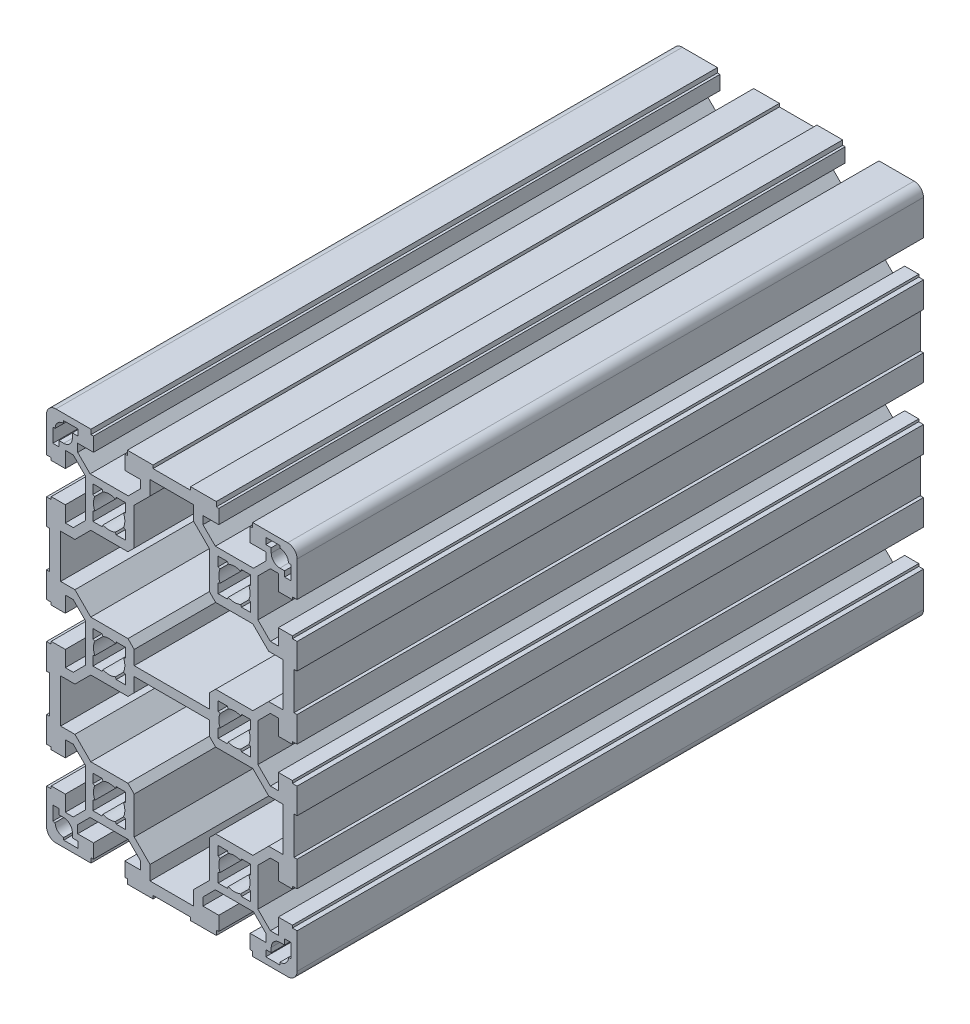
SolidWorks part; units mm, degrees
ref_plane "Front Plane" through (0, 0, 0) normal (0, 0, 1) x (1, 0, 0)
ref_plane "Top Plane" through (0, 0, 0) normal (0, 1, 0) x (1, 0, 0)
ref_plane "Right Plane" through (0, 0, 0) normal (1, 0, 0) x (0, 0, -1)
sketch "Sketch1" plane through (0, 0, 0) normal (0, 0, 1) x (1, 0, 0)
  line L0 (27.5, 46.0858) -> (31.4642, 50.05)
  line L1 (31.4642, 50.05) -> (34, 50.05)
  line L2 (34, 50.05) -> (34, 45)
  line L3 (34, 45) -> (38.5, 45)
  line L4 (38.5, 45) -> (38.5, 45.8)
  line L5 (38.5, 45.8) -> (40, 45.8)
  line L6 (40, 45.8) -> (40, 57)
  line L7 (37, 60) -> (25.8, 60)
  line L8 (25.8, 60) -> (25.8, 58.5)
  line L9 (25.8, 58.5) -> (25, 58.5)
  line L10 (25, 58.5) -> (25, 54)
  line L11 (25, 54) -> (30.05, 54)
  line L12 (30.05, 54) -> (30.05, 51.4642)
  line L13 (30.05, 51.4642) -> (26.0858, 47.5)
  line L14 (26.0858, 47.5) -> (13.9142, 47.5)
  line L15 (13.9142, 47.5) -> (9.95, 51.4642)
  line L16 (9.95, 51.4642) -> (9.95, 54)
  line L17 (9.95, 54) -> (15, 54)
  line L18 (15, 54) -> (15, 58.5)
  line L19 (15, 58.5) -> (14.2, 58.5)
  line L20 (14.2, 58.5) -> (14.2, 60)
  line L21 (14.2, 60) -> (6, 60)
  line L22 (6, 60) -> (6, 59)
  line L23 (27.5, -6.0858) -> (27.5, 6.0858)
  line L24 (27.5, 6.0858) -> (31.4642, 10.05)
  line L25 (31.4642, 10.05) -> (34, 10.05)
  line L26 (34, 10.05) -> (34, 5)
  line L27 (34, 5) -> (38.5, 5)
  line L28 (38.5, 5) -> (38.5, 5.8)
  line L29 (38.5, 5.8) -> (40, 5.8)
  line L30 (40, 5.8) -> (40, 14)
  line L31 (40, 14) -> (39, 14)
  line L32 (39, 14) -> (39, 26)
  line L33 (39, 26) -> (40, 26)
  line L34 (40, 26) -> (40, 34.2)
  line L35 (40, 34.2) -> (38.5, 34.2)
  line L36 (38.5, 34.2) -> (38.5, 35)
  line L37 (38.5, 35) -> (34, 35)
  line L38 (34, 35) -> (34, 29.95)
  line L39 (34, 29.95) -> (31.4642, 29.95)
  line L40 (31.4642, 29.95) -> (27.5, 33.9142)
  line L41 (27.5, 33.9142) -> (27.5, 46.0858)
  line L42 (12, 45.8787) -> (6.95, 50.9287)
  line L43 (6.95, 50.9287) -> (6.95, 55.5)
  line L44 (12, 1.5) -> (12, 6)
  line L45 (12, 6) -> (14, 8)
  line L46 (14, 8) -> (25.8787, 8)
  line L47 (25.8787, 8) -> (30.9287, 13.05)
  line L48 (30.9287, 13.05) -> (35.5, 13.05)
  line L49 (35.5, 13.05) -> (35.5, 26.95)
  line L50 (35.5, 26.95) -> (30.9287, 26.95)
  line L51 (-14.8, 2.2603) -> (-15.4145, 1.9932)
  line L52 (-14.8, 5.2) -> (-14.8, 2.2603)
  line L53 (-17.7397, 5.2) -> (-14.8, 5.2)
  line L54 (-18.0068, 4.5855) -> (-17.7397, 5.2)
  line L55 (-22.2603, 5.2) -> (-21.9932, 4.5855)
  line L56 (-25.2, 5.2) -> (-22.2603, 5.2)
  line L57 (-25.2, 2.2603) -> (-25.2, 5.2)
  line L58 (-24.5855, 1.9932) -> (-25.2, 2.2603)
  line L59 (30.9287, 26.95) -> (25.8787, 32)
  line L60 (25.8787, 32) -> (14, 32)
  line L61 (14, 32) -> (12, 34)
  line L62 (12, 34) -> (12, 45.8787)
  line L63 (34.5, 51.75) -> (36, 51.75)
  line L64 (36, 51.75) -> (36, 50)
  line L65 (36, 50) -> (38, 50)
  line L66 (38, 50) -> (38, 54.5)
  line L67 (38, 54.5) -> (37.25, 54.5)
  line L68 (34.5, 57.25) -> (34.5, 58)
  line L69 (34.5, 58) -> (30, 58)
  line L70 (30, 58) -> (30, 56)
  line L71 (30, 56) -> (31.75, 56)
  line L72 (31.75, 56) -> (31.75, 54.5)
  line L73 (17.7397, 34.8) -> (18.0068, 35.4145)
  line L74 (21.9932, 35.4145) -> (22.2603, 34.8)
  line L75 (22.2603, 34.8) -> (25.2, 34.8)
  line L76 (25.2, 34.8) -> (25.2, 37.7397)
  line L77 (25.2, 37.7397) -> (24.5855, 38.0068)
  line L78 (24.5855, 41.9932) -> (25.2, 42.2603)
  line L79 (25.2, 42.2603) -> (25.2, 45.2)
  line L80 (-14.8, 34.8) -> (-17.7397, 34.8)
  line L81 (-14.8, 37.7397) -> (-14.8, 34.8)
  line L82 (-15.4145, 38.0068) -> (-14.8, 37.7397)
  line L83 (-14.8, 42.2603) -> (-15.4145, 41.9932)
  line L84 (-14.8, 45.2) -> (-14.8, 42.2603)
  line L85 (-17.7397, 45.2) -> (-14.8, 45.2)
  line L86 (-18.0068, 44.5855) -> (-17.7397, 45.2)
  line L87 (-22.2603, 45.2) -> (-21.9932, 44.5855)
  line L88 (-25.2, 45.2) -> (-22.2603, 45.2)
  line L89 (-25.2, 42.2603) -> (-25.2, 45.2)
  line L90 (-24.5855, 41.9932) -> (-25.2, 42.2603)
  line L91 (-25.2, 37.7397) -> (-24.5855, 38.0068)
  line L92 (-25.2, 34.8) -> (-25.2, 37.7397)
  line L93 (-22.2603, 34.8) -> (-25.2, 34.8)
  line L94 (-21.9932, 35.4145) -> (-22.2603, 34.8)
  line L95 (-17.7397, 34.8) -> (-18.0068, 35.4145)
  line L96 (25.2, 45.2) -> (22.2603, 45.2)
  line L97 (22.2603, 45.2) -> (21.9932, 44.5855)
  line L98 (18.0068, 44.5855) -> (17.7397, 45.2)
  line L99 (17.7397, 45.2) -> (14.8, 45.2)
  line L100 (14.8, 45.2) -> (14.8, 42.2603)
  line L101 (14.8, 42.2603) -> (15.4145, 41.9932)
  line L102 (15.4145, 38.0068) -> (14.8, 37.7397)
  line L103 (14.8, 37.7397) -> (14.8, 34.8)
  line L104 (14.8, 34.8) -> (17.7397, 34.8)
  line L105 (24.5855, 1.9932) -> (25.2, 2.2603)
  line L106 (25.2, 2.2603) -> (25.2, 5.2)
  line L107 (25.2, 5.2) -> (22.2603, 5.2)
  line L108 (22.2603, 5.2) -> (21.9932, 4.5855)
  line L109 (18.0068, 4.5855) -> (17.7397, 5.2)
  line L110 (17.7397, 5.2) -> (14.8, 5.2)
  line L111 (14.8, 5.2) -> (14.8, 2.2603)
  line L112 (14.8, 2.2603) -> (15.4145, 1.9932)
  line L113 (-27.5, -46.0858) -> (-31.4642, -50.05)
  line L114 (-31.4642, -50.05) -> (-34, -50.05)
  line L115 (-34, -50.05) -> (-34, -45)
  line L116 (-34, -45) -> (-38.5, -45)
  line L117 (-38.5, -45) -> (-38.5, -45.8)
  line L118 (-38.5, -45.8) -> (-40, -45.8)
  line L119 (-40, -45.8) -> (-40, -57)
  line L120 (-37, -60) -> (-25.8, -60)
  line L121 (-25.8, -60) -> (-25.8, -58.5)
  line L122 (-25.8, -58.5) -> (-25, -58.5)
  line L123 (-25, -58.5) -> (-25, -54)
  line L124 (-25, -54) -> (-30.05, -54)
  line L125 (-30.05, -54) -> (-30.05, -51.4642)
  line L126 (-31.75, 56) -> (-31.75, 54.5)
  line L127 (-30, 56) -> (-31.75, 56)
  line L128 (-30, 58) -> (-30, 56)
  line L129 (-34.5, 58) -> (-30, 58)
  line L130 (-34.5, 57.25) -> (-34.5, 58)
  line L131 (-38, 54.5) -> (-37.25, 54.5)
  line L132 (-38, 50) -> (-38, 54.5)
  line L133 (-36, 50) -> (-38, 50)
  line L134 (-36, 51.75) -> (-36, 50)
  line L135 (-34.5, 51.75) -> (-36, 51.75)
  line L136 (-30.05, -51.4642) -> (-26.0858, -47.5)
  line L137 (-26.0858, -47.5) -> (-13.9142, -47.5)
  line L138 (-13.9142, -47.5) -> (-9.95, -51.4642)
  line L139 (-9.95, -51.4642) -> (-9.95, -54)
  line L140 (-9.95, -54) -> (-15, -54)
  line L141 (-15, -54) -> (-15, -58.5)
  line L142 (-15, -58.5) -> (-14.2, -58.5)
  line L143 (-14.2, -58.5) -> (-14.2, -60)
  line L144 (-14.2, -60) -> (-6, -60)
  line L145 (-6, -60) -> (-6, -59)
  line L146 (-6, -59) -> (6, -59)
  line L147 (-27.5, -6.0858) -> (-31.4642, -10.05)
  line L148 (-31.4642, -10.05) -> (-34, -10.05)
  line L149 (-34, -10.05) -> (-34, -5)
  line L150 (-34, -5) -> (-38.5, -5)
  line L151 (-38.5, -5) -> (-38.5, -5.8)
  line L152 (-38.5, -5.8) -> (-40, -5.8)
  line L153 (-40, -5.8) -> (-40, -14)
  line L154 (-40, -14) -> (-39, -14)
  line L155 (-39, -14) -> (-39, -26)
  line L156 (-39, -26) -> (-40, -26)
  line L157 (-40, -26) -> (-40, -34.2)
  line L158 (-40, -34.2) -> (-38.5, -34.2)
  line L159 (-38.5, -34.2) -> (-38.5, -35)
  line L160 (-38.5, -35) -> (-34, -35)
  line L161 (-34, -35) -> (-34, -29.95)
  line L162 (-34, -29.95) -> (-31.4642, -29.95)
  line L163 (-31.4642, -29.95) -> (-27.5, -33.9142)
  line L164 (-12, 34) -> (-12, 45.8787)
  line L165 (-14, 32) -> (-12, 34)
  line L166 (-25.8787, 32) -> (-14, 32)
  line L167 (-30.9287, 26.95) -> (-25.8787, 32)
  line L168 (-35.5, 26.95) -> (-30.9287, 26.95)
  line L169 (-35.5, 13.05) -> (-35.5, 26.95)
  line L170 (-30.9287, 13.05) -> (-35.5, 13.05)
  line L171 (-25.8787, 8) -> (-30.9287, 13.05)
  line L172 (-14, 8) -> (-25.8787, 8)
  line L173 (-12, 6) -> (-14, 8)
  line L174 (-12, 1.5) -> (-12, 6)
  line L175 (12, 1.5) -> (-12, 1.5)
  line L176 (-27.5, -33.9142) -> (-27.5, -46.0858)
  line L177 (-12, -45.8787) -> (-6.95, -50.9287)
  line L178 (-6.95, -50.9287) -> (-6.95, -55.5)
  line L179 (-6.95, -55.5) -> (6.95, -55.5)
  line L180 (12, -1.5) -> (-12, -1.5)
  line L181 (-12, -1.5) -> (-12, -6)
  line L182 (-12, -6) -> (-14, -8)
  line L183 (-14, -8) -> (-25.8787, -8)
  line L184 (-25.8787, -8) -> (-30.9287, -13.05)
  line L185 (-30.9287, -13.05) -> (-35.5, -13.05)
  line L186 (-35.5, -13.05) -> (-35.5, -26.95)
  line L187 (-35.5, -26.95) -> (-30.9287, -26.95)
  line L188 (-30.9287, -26.95) -> (-25.8787, -32)
  line L189 (-6.95, 55.5) -> (6.95, 55.5)
  line L190 (-6.95, 50.9287) -> (-6.95, 55.5)
  line L191 (-12, 45.8787) -> (-6.95, 50.9287)
  line L192 (-27.5, 33.9142) -> (-27.5, 46.0858)
  line L193 (-31.4642, 29.95) -> (-27.5, 33.9142)
  line L194 (-34, 29.95) -> (-31.4642, 29.95)
  line L195 (-34, 35) -> (-34, 29.95)
  line L196 (-38.5, 35) -> (-34, 35)
  line L197 (-38.5, 34.2) -> (-38.5, 35)
  line L198 (-40, 34.2) -> (-38.5, 34.2)
  line L199 (-40, 26) -> (-40, 34.2)
  line L200 (-39, 26) -> (-40, 26)
  line L201 (-39, 14) -> (-39, 26)
  line L202 (-40, 14) -> (-39, 14)
  line L203 (-40, 5.8) -> (-40, 14)
  line L204 (-38.5, 5.8) -> (-40, 5.8)
  line L205 (-38.5, 5) -> (-38.5, 5.8)
  line L206 (-34, 5) -> (-38.5, 5)
  line L207 (-34, 10.05) -> (-34, 5)
  line L208 (-31.4642, 10.05) -> (-34, 10.05)
  line L209 (-27.5, 6.0858) -> (-31.4642, 10.05)
  line L210 (-27.5, -6.0858) -> (-27.5, 6.0858)
  line L211 (-25.8787, -32) -> (-14, -32)
  line L212 (-14, -32) -> (-12, -34)
  line L213 (-12, -34) -> (-12, -45.8787)
  line L214 (-34.5, -51.75) -> (-36, -51.75)
  line L215 (-36, -51.75) -> (-36, -50)
  line L216 (-36, -50) -> (-38, -50)
  line L217 (-38, -50) -> (-38, -54.5)
  line L218 (-38, -54.5) -> (-37.25, -54.5)
  line L219 (-34.5, -57.25) -> (-34.5, -58)
  line L220 (-34.5, -58) -> (-30, -58)
  line L221 (-30, -58) -> (-30, -56)
  line L222 (-30, -56) -> (-31.75, -56)
  line L223 (-31.75, -56) -> (-31.75, -54.5)
  line L224 (14.8, -2.2603) -> (15.4145, -1.9932)
  line L225 (14.8, -5.2) -> (14.8, -2.2603)
  line L226 (17.7397, -5.2) -> (14.8, -5.2)
  line L227 (18.0068, -4.5855) -> (17.7397, -5.2)
  line L228 (22.2603, -5.2) -> (21.9932, -4.5855)
  line L229 (25.2, -5.2) -> (22.2603, -5.2)
  line L230 (25.2, -2.2603) -> (25.2, -5.2)
  line L231 (24.5855, -1.9932) -> (25.2, -2.2603)
  line L232 (14.8, -34.8) -> (17.7397, -34.8)
  line L233 (14.8, -37.7397) -> (14.8, -34.8)
  line L234 (15.4145, -38.0068) -> (14.8, -37.7397)
  line L235 (14.8, -42.2603) -> (15.4145, -41.9932)
  line L236 (14.8, -45.2) -> (14.8, -42.2603)
  line L237 (17.7397, -45.2) -> (14.8, -45.2)
  line L238 (18.0068, -44.5855) -> (17.7397, -45.2)
  line L239 (22.2603, -45.2) -> (21.9932, -44.5855)
  line L240 (25.2, -45.2) -> (22.2603, -45.2)
  line L241 (-17.7397, -34.8) -> (-18.0068, -35.4145)
  line L242 (-21.9932, -35.4145) -> (-22.2603, -34.8)
  line L243 (-22.2603, -34.8) -> (-25.2, -34.8)
  line L244 (-25.2, -34.8) -> (-25.2, -37.7397)
  line L245 (-25.2, -37.7397) -> (-24.5855, -38.0068)
  line L246 (-24.5855, -41.9932) -> (-25.2, -42.2603)
  line L247 (-25.2, -42.2603) -> (-25.2, -45.2)
  line L248 (-25.2, -45.2) -> (-22.2603, -45.2)
  line L249 (-22.2603, -45.2) -> (-21.9932, -44.5855)
  line L250 (-18.0068, -44.5855) -> (-17.7397, -45.2)
  line L251 (-17.7397, -45.2) -> (-14.8, -45.2)
  line L252 (-14.8, -45.2) -> (-14.8, -42.2603)
  line L253 (-14.8, -42.2603) -> (-15.4145, -41.9932)
  line L254 (-15.4145, -38.0068) -> (-14.8, -37.7397)
  line L255 (-14.8, -37.7397) -> (-14.8, -34.8)
  line L256 (-14.8, -34.8) -> (-17.7397, -34.8)
  line L257 (25.2, -42.2603) -> (25.2, -45.2)
  line L258 (24.5855, -41.9932) -> (25.2, -42.2603)
  line L259 (25.2, -37.7397) -> (24.5855, -38.0068)
  line L260 (25.2, -34.8) -> (25.2, -37.7397)
  line L261 (22.2603, -34.8) -> (25.2, -34.8)
  line L262 (21.9932, -35.4145) -> (22.2603, -34.8)
  line L263 (17.7397, -34.8) -> (18.0068, -35.4145)
  line L264 (31.75, -56) -> (31.75, -54.5)
  line L265 (30, -56) -> (31.75, -56)
  line L266 (30, -58) -> (30, -56)
  line L267 (34.5, -58) -> (30, -58)
  line L268 (34.5, -57.25) -> (34.5, -58)
  line L269 (38, -54.5) -> (37.25, -54.5)
  line L270 (38, -50) -> (38, -54.5)
  line L271 (36, -50) -> (38, -50)
  line L272 (36, -51.75) -> (36, -50)
  line L273 (34.5, -51.75) -> (36, -51.75)
  line L274 (12, -34) -> (12, -45.8787)
  line L275 (14, -32) -> (12, -34)
  line L276 (25.8787, -32) -> (14, -32)
  line L277 (30.9287, -26.95) -> (25.8787, -32)
  line L278 (-24.5855, -1.9932) -> (-25.2, -2.2603)
  line L279 (-25.2, -2.2603) -> (-25.2, -5.2)
  line L280 (-25.2, -5.2) -> (-22.2603, -5.2)
  line L281 (-22.2603, -5.2) -> (-21.9932, -4.5855)
  line L282 (-18.0068, -4.5855) -> (-17.7397, -5.2)
  line L283 (-17.7397, -5.2) -> (-14.8, -5.2)
  line L284 (-14.8, -5.2) -> (-14.8, -2.2603)
  line L285 (-14.8, -2.2603) -> (-15.4145, -1.9932)
  line L286 (35.5, -26.95) -> (30.9287, -26.95)
  line L287 (35.5, -13.05) -> (35.5, -26.95)
  line L288 (30.9287, -13.05) -> (35.5, -13.05)
  line L289 (25.8787, -8) -> (30.9287, -13.05)
  line L290 (14, -8) -> (25.8787, -8)
  line L291 (12, -6) -> (14, -8)
  line L292 (12, -1.5) -> (12, -6)
  line L293 (6.95, -50.9287) -> (6.95, -55.5)
  line L294 (12, -45.8787) -> (6.95, -50.9287)
  line L295 (27.5, -33.9142) -> (27.5, -46.0858)
  line L296 (31.4642, -29.95) -> (27.5, -33.9142)
  line L297 (34, -29.95) -> (31.4642, -29.95)
  line L298 (34, -35) -> (34, -29.95)
  line L299 (38.5, -35) -> (34, -35)
  line L300 (38.5, -34.2) -> (38.5, -35)
  line L301 (40, -34.2) -> (38.5, -34.2)
  line L302 (40, -26) -> (40, -34.2)
  line L303 (39, -26) -> (40, -26)
  line L304 (39, -14) -> (39, -26)
  line L305 (40, -14) -> (39, -14)
  line L306 (40, -5.8) -> (40, -14)
  line L307 (38.5, -5.8) -> (40, -5.8)
  line L308 (38.5, -5) -> (38.5, -5.8)
  line L309 (34, -5) -> (38.5, -5)
  line L310 (34, -10.05) -> (34, -5)
  line L311 (31.4642, -10.05) -> (34, -10.05)
  line L312 (27.5, -6.0858) -> (31.4642, -10.05)
  line L313 (6, -60) -> (6, -59)
  line L314 (14.2, -60) -> (6, -60)
  line L315 (14.2, -58.5) -> (14.2, -60)
  line L316 (15, -58.5) -> (14.2, -58.5)
  line L317 (15, -54) -> (15, -58.5)
  line L318 (9.95, -54) -> (15, -54)
  line L319 (9.95, -51.4642) -> (9.95, -54)
  line L320 (13.9142, -47.5) -> (9.95, -51.4642)
  line L321 (26.0858, -47.5) -> (13.9142, -47.5)
  line L322 (30.05, -51.4642) -> (26.0858, -47.5)
  line L323 (30.05, -54) -> (30.05, -51.4642)
  line L324 (25, -54) -> (30.05, -54)
  line L325 (25, -58.5) -> (25, -54)
  line L326 (25.8, -58.5) -> (25, -58.5)
  line L327 (25.8, -60) -> (25.8, -58.5)
  line L328 (37, -60) -> (25.8, -60)
  line L329 (40, -45.8) -> (40, -57)
  line L330 (38.5, -45.8) -> (40, -45.8)
  line L331 (38.5, -45) -> (38.5, -45.8)
  line L332 (34, -45) -> (38.5, -45)
  line L333 (34, -50.05) -> (34, -45)
  line L334 (31.4642, -50.05) -> (34, -50.05)
  line L335 (27.5, -46.0858) -> (31.4642, -50.05)
  line L336 (-6, 59) -> (6, 59)
  line L337 (-6, 60) -> (-6, 59)
  line L338 (-14.2, 60) -> (-6, 60)
  line L339 (-14.2, 58.5) -> (-14.2, 60)
  line L340 (-15, 58.5) -> (-14.2, 58.5)
  line L341 (-15, 54) -> (-15, 58.5)
  line L342 (-9.95, 54) -> (-15, 54)
  line L343 (-9.95, 51.4642) -> (-9.95, 54)
  line L344 (-13.9142, 47.5) -> (-9.95, 51.4642)
  line L345 (-26.0858, 47.5) -> (-13.9142, 47.5)
  line L346 (-30.05, 51.4642) -> (-26.0858, 47.5)
  line L347 (-30.05, 54) -> (-30.05, 51.4642)
  line L348 (-25, 54) -> (-30.05, 54)
  line L349 (-25, 58.5) -> (-25, 54)
  line L350 (-25.8, 58.5) -> (-25, 58.5)
  line L351 (-25.8, 60) -> (-25.8, 58.5)
  line L352 (-37, 60) -> (-25.8, 60)
  line L353 (-40, 45.8) -> (-40, 57)
  line L354 (-38.5, 45.8) -> (-40, 45.8)
  line L355 (-38.5, 45) -> (-38.5, 45.8)
  line L356 (-34, 45) -> (-38.5, 45)
  line L357 (-34, 50.05) -> (-34, 45)
  line L358 (-31.4642, 50.05) -> (-34, 50.05)
  line L359 (-27.5, 46.0858) -> (-31.4642, 50.05)
  line L361 (0, -1.5) -> (0, 87.2985) construction
  line L362 (0, -1.5) -> (0, -80.6537) construction
  arc A0 (37, 60) -> (40, 57) centre (37, 57) cw
  arc A1 (34.5, 57.25) -> (37.25, 54.5) centre (34.5, 54.5) cw
  arc A2 (34.5, 51.75) -> (31.75, 54.5) centre (34.5, 54.5) cw
  arc A3 (21.9932, 35.4145) -> (18.0068, 35.4145) centre (20, 40) cw
  arc A4 (24.5855, 41.9932) -> (24.5855, 38.0068) centre (20, 40) cw
  arc A5 (18.0068, 44.5855) -> (21.9932, 44.5855) centre (20, 40) cw
  arc A6 (15.4145, 38.0068) -> (15.4145, 41.9932) centre (20, 40) cw
  arc A7 (24.5855, 1.9932) -> (24.5855, -1.9932) centre (20, 0) cw
  arc A8 (18.0068, 4.5855) -> (21.9932, 4.5855) centre (20, 0) cw
  arc A9 (15.4145, -1.9932) -> (15.4145, 1.9932) centre (20, 0) cw
  arc A10 (-37, -60) -> (-40, -57) centre (-37, -57) cw
  arc A11 (-34.5, -57.25) -> (-37.25, -54.5) centre (-34.5, -54.5) cw
  arc A12 (-15.4145, -1.9932) -> (-15.4145, 1.9932) centre (-20, 0) ccw
  arc A13 (-18.0068, 4.5855) -> (-21.9932, 4.5855) centre (-20, 0) ccw
  arc A14 (-24.5855, 1.9932) -> (-24.5855, -1.9932) centre (-20, 0) ccw
  arc A15 (-34.5, -51.75) -> (-31.75, -54.5) centre (-34.5, -54.5) cw
  arc A16 (-21.9932, -35.4145) -> (-18.0068, -35.4145) centre (-20, -40) cw
  arc A17 (-24.5855, -41.9932) -> (-24.5855, -38.0068) centre (-20, -40) cw
  arc A18 (-18.0068, -44.5855) -> (-21.9932, -44.5855) centre (-20, -40) cw
  arc A19 (-15.4145, -38.0068) -> (-15.4145, -41.9932) centre (-20, -40) cw
  arc A20 (-15.4145, 38.0068) -> (-15.4145, 41.9932) centre (-20, 40) ccw
  arc A21 (-18.0068, 44.5855) -> (-21.9932, 44.5855) centre (-20, 40) ccw
  arc A22 (-24.5855, 41.9932) -> (-24.5855, 38.0068) centre (-20, 40) ccw
  arc A23 (-21.9932, 35.4145) -> (-18.0068, 35.4145) centre (-20, 40) ccw
  arc A24 (-18.0068, -4.5855) -> (-21.9932, -4.5855) centre (-20, 0) cw
  arc A25 (18.0068, -4.5855) -> (21.9932, -4.5855) centre (20, 0) ccw
  arc A26 (15.4145, -38.0068) -> (15.4145, -41.9932) centre (20, -40) ccw
  arc A27 (18.0068, -44.5855) -> (21.9932, -44.5855) centre (20, -40) ccw
  arc A28 (24.5855, -41.9932) -> (24.5855, -38.0068) centre (20, -40) ccw
  arc A29 (21.9932, -35.4145) -> (18.0068, -35.4145) centre (20, -40) ccw
  arc A30 (-34.5, 51.75) -> (-31.75, 54.5) centre (-34.5, 54.5) ccw
  arc A31 (-34.5, 57.25) -> (-37.25, 54.5) centre (-34.5, 54.5) ccw
  arc A32 (34.5, -51.75) -> (31.75, -54.5) centre (34.5, -54.5) ccw
  arc A33 (34.5, -57.25) -> (37.25, -54.5) centre (34.5, -54.5) ccw
  arc A34 (37, -60) -> (40, -57) centre (37, -57) ccw
  arc A35 (-37, 60) -> (-40, 57) centre (-37, 57) ccw
  point P79 (0, 59)
  point P102 (0, 55.5)
  point P104 (0, 1.5)
  point P227 (0, -55.5)
  point P228 (0, -59)
  point P254 (-27.5, 0)
  point P396 (27.5, 0)
  dimension "D3" = 10
  dimension "D1" = 120
  dimension "D2" = 80
extrude "Base-Extrude" add sketch "Sketch1" against normal blind 200
